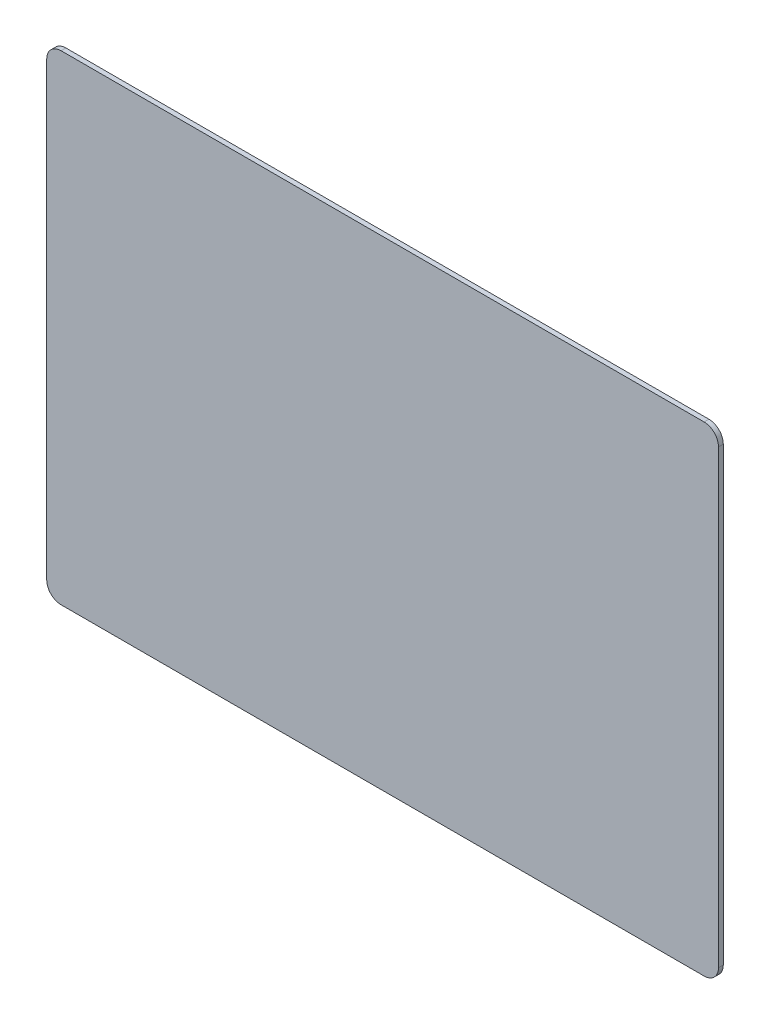
SolidWorks part; units mm, degrees
ref_plane "Ebene vorne" through (0, 0, 0) normal (0, 0, 1) x (1, 0, 0)
ref_plane "Ebene oben" through (0, 0, 0) normal (0, 1, 0) x (1, 0, 0)
ref_plane "Ebene rechts" through (0, 0, 0) normal (1, 0, 0) x (0, 0, -1)
sketch "Skizze1" plane through (0, 0, 0) normal (0, 0, 1) x (1, 0, 0)
  line L1 (-70, -50) -> (70, -50)
  line L2 (-70, -50) -> (-70, 50)
  line L3 (-70, 50) -> (70, 50)
  line L4 (70, -50) -> (70, 50)
  line L5 (-70, -50) -> (70, 50) construction
  line L6 (-70, 50) -> (70, -50) construction
  point P0 (0, 0)
  dimension "D1" = 140
  dimension "D2" = 100
extrude "Aufsatz-Linear austragen1" add sketch "Skizze1" against normal blind 1
fillet "Verrundung1" radius 3 4 edges at (-70, 50, -0.5) (-70, -50, -0.5) (70, -50, -0.5) (70, 50, -0.5)
